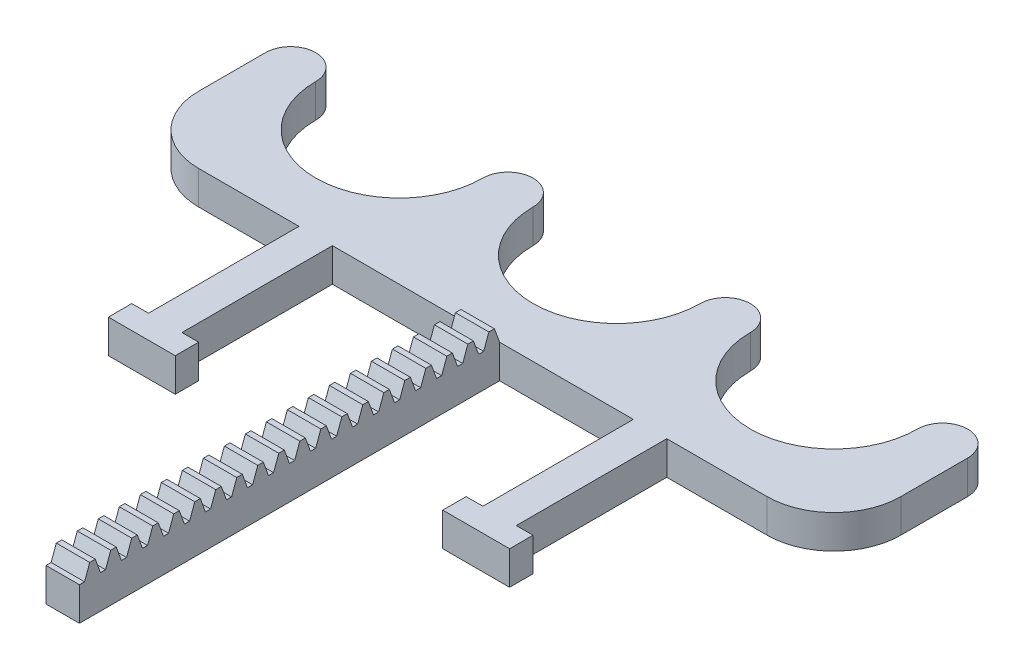
SolidWorks part; units mm, degrees
ref_plane "Plan de face" through (0, 0, 0) normal (0, 0, 1) x (1, 0, 0)
ref_plane "Plan de dessus" through (0, 0, 0) normal (0, 1, 0) x (1, 0, 0)
ref_plane "Plan de droite" through (0, 0, 0) normal (1, 0, 0) x (0, 0, -1)
sketch "Esquisse1" plane through (0, 0, 0) normal (0, 1, 0) x (1, 0, 0)
  line L0 (130, 40) -> (145, 40) construction
  line L1 (0, 0) -> (210, 0)
  line L2 (0, 0) -> (0, 40)
  line L3 (0, 40) -> (15, 40) construction
  line L4 (210, 0) -> (210, 40)
  line L5 (195, 40) -> (210, 40) construction
  line L6 (15, 40) -> (65, 40) construction
  line L7 (80, 40) -> (130, 40) construction
  line L8 (145, 40) -> (195, 40) construction
  line L9 (65, 40) -> (80, 40) construction
  arc A0 (15, 40) -> (65, 40) centre (40, 40) ccw
  arc A1 (80, 40) -> (130, 40) centre (105, 40) ccw
  arc A2 (145, 40) -> (195, 40) centre (170, 40) ccw
  arc A3 (130, 40) -> (145, 40) centre (137.5, 40) cw
  arc A4 (195, 40) -> (210, 40) centre (202.5, 40) cw
  arc A5 (65, 40) -> (80, 40) centre (72.5, 40) cw
  arc A6 (0, 40) -> (15, 40) centre (7.5, 40) cw
  point P17 (105, 40)
  point P19 (170, 40)
  dimension "D2" = 25
  dimension "D4" = 25
  dimension "D5" = 25
  dimension "D1" = 15
  dimension "D3" = 40
  dimension "D6" = 15
  dimension "D7" = 15
  dimension "D8" = 15
extrude "Boss.-Extru.1" add sketch "Esquisse1" along normal blind 10
sketch "Esquisse2" plane through (0, 10, 0) normal (0, 1, 0) x (1, 0, 0)
  line L0 (0, 0) -> (210, 0) construction
  line L1 (50, 0) -> (60, 0)
  line L2 (50, 0) -> (50, -45)
  line L3 (50, -45) -> (60, -45)
  line L4 (60, 0) -> (60, -45)
  line L5 (0, 40) -> (0, 0) construction
  line L6 (150, 0) -> (160, 0)
  line L7 (150, 0) -> (150, -45)
  line L8 (150, -45) -> (160, -45)
  line L9 (160, 0) -> (160, -45)
  line L10 (100, 0) -> (110, 0)
  line L11 (100, 0) -> (100, -45)
  line L12 (100, -45) -> (110, -45)
  line L13 (110, 0) -> (110, -45)
  line L14 (210, 0) -> (210, 40) construction
  line L16 (45, -45) -> (65, -45)
  line L17 (45, -45) -> (45, -52)
  line L18 (45, -52) -> (65, -52)
  line L19 (65, -45) -> (65, -52)
  line L24 (145, -45) -> (165, -45)
  line L25 (145, -45) -> (145, -52)
  line L26 (145, -52) -> (165, -52)
  line L27 (165, -45) -> (165, -52)
  point P18 (105, 0)
  point P19 (105, 0)
  point P24 (55, -45)
  point P25 (55, -45)
  point P36 (155, -45)
  point P37 (155, -45)
  dimension "D1" = 10
  dimension "D2" = 10
  dimension "D3" = 10
  dimension "D4" = 45
  dimension "D5" = 50
  dimension "D6" = 50
  dimension "D7" = 7
  dimension "D8" = 20
extrude "Boss.-Extru.2" add sketch "Esquisse2" against normal blind 10
fillet "Congé1" radius 20 2 edges at (210, 5, 0) (0, 5, 0)
sketch "Esquisse3" plane through (100, 0, 0) normal (-1, 0, 0) x (0, 0, 1)
  line L0 (2.378, 14.25) -> (2.378, 12.25) construction
  line L1 (-2.1293, 12.25) -> (5.817, 12.25) construction
  line L2 (2.378, 12.25) -> (5.4445, 13.3661) construction
  line L3 (3.209, 14.25) -> (4.7559, 10)
  line L4 (1.5469, 14.25) -> (0, 10)
  line L5 (1.5469, 14.25) -> (3.209, 14.25)
  line L6 (0, 10) -> (6.283, 10) construction
  line L7 (4.7559, 10) -> (6.283, 10)
  line L8 (7.8299, 14.25) -> (9.492, 14.25)
  line L9 (7.8299, 14.25) -> (6.283, 10)
  line L10 (9.492, 14.25) -> (11.0389, 10)
  line L11 (11.0389, 10) -> (12.566, 10)
  line L12 (14.1129, 14.25) -> (15.775, 14.25)
  line L13 (14.1129, 14.25) -> (12.566, 10)
  line L14 (15.775, 14.25) -> (17.3219, 10)
  line L15 (17.3219, 10) -> (18.849, 10)
  line L16 (20.3959, 14.25) -> (22.058, 14.25)
  line L17 (20.3959, 14.25) -> (18.849, 10)
  line L18 (22.058, 14.25) -> (23.6049, 10)
  line L19 (23.6049, 10) -> (25.132, 10)
  line L20 (26.6789, 14.25) -> (28.341, 14.25)
  line L21 (26.6789, 14.25) -> (25.132, 10)
  line L22 (28.341, 14.25) -> (29.8879, 10)
  line L23 (29.8879, 10) -> (31.415, 10)
  line L24 (32.9619, 14.25) -> (34.624, 14.25)
  line L25 (32.9619, 14.25) -> (31.415, 10)
  line L26 (34.624, 14.25) -> (36.1709, 10)
  line L27 (36.1709, 10) -> (37.698, 10)
  line L28 (39.2449, 14.25) -> (40.907, 14.25)
  line L29 (39.2449, 14.25) -> (37.698, 10)
  line L30 (40.907, 14.25) -> (42.4539, 10)
  line L31 (42.4539, 10) -> (43.981, 10)
  line L32 (0, 10) -> (0, 0)
  line L33 (0, 0) -> (125.66, 0)
  line L35 (45.5279, 14.25) -> (47.19, 14.25)
  line L36 (45.5279, 14.25) -> (43.981, 10)
  line L37 (47.19, 14.25) -> (48.7369, 10)
  line L38 (48.7369, 10) -> (50.264, 10)
  line L39 (51.8109, 14.25) -> (53.473, 14.25)
  line L40 (51.8109, 14.25) -> (50.264, 10)
  line L41 (53.473, 14.25) -> (55.0199, 10)
  line L42 (55.0199, 10) -> (56.547, 10)
  line L43 (58.0939, 14.25) -> (59.756, 14.25)
  line L44 (58.0939, 14.25) -> (56.547, 10)
  line L45 (59.756, 14.25) -> (61.3029, 10)
  line L46 (61.3029, 10) -> (62.83, 10)
  line L47 (64.3769, 14.25) -> (66.039, 14.25)
  line L48 (64.3769, 14.25) -> (62.83, 10)
  line L49 (66.039, 14.25) -> (67.5859, 10)
  line L50 (67.5859, 10) -> (69.113, 10)
  line L51 (70.6599, 14.25) -> (72.322, 14.25)
  line L52 (70.6599, 14.25) -> (69.113, 10)
  line L53 (72.322, 14.25) -> (73.8689, 10)
  line L54 (73.8689, 10) -> (75.396, 10)
  line L55 (76.9429, 14.25) -> (78.605, 14.25)
  line L56 (76.9429, 14.25) -> (75.396, 10)
  line L57 (78.605, 14.25) -> (80.1519, 10)
  line L58 (80.1519, 10) -> (81.679, 10)
  line L59 (83.2259, 14.25) -> (84.888, 14.25)
  line L60 (83.2259, 14.25) -> (81.679, 10)
  line L61 (84.888, 14.25) -> (86.4349, 10)
  line L62 (86.4349, 10) -> (87.962, 10)
  line L63 (89.5089, 14.25) -> (91.171, 14.25)
  line L64 (89.5089, 14.25) -> (87.962, 10)
  line L65 (91.171, 14.25) -> (92.7179, 10)
  line L66 (92.7179, 10) -> (94.245, 10)
  line L67 (95.7919, 14.25) -> (97.454, 14.25)
  line L68 (95.7919, 14.25) -> (94.245, 10)
  line L69 (97.454, 14.25) -> (99.0009, 10)
  line L70 (99.0009, 10) -> (100.528, 10)
  line L71 (102.0749, 14.25) -> (103.737, 14.25)
  line L72 (102.0749, 14.25) -> (100.528, 10)
  line L73 (103.737, 14.25) -> (105.2839, 10)
  line L74 (105.2839, 10) -> (106.811, 10)
  line L75 (108.3579, 14.25) -> (110.02, 14.25)
  line L76 (108.3579, 14.25) -> (106.811, 10)
  line L77 (110.02, 14.25) -> (111.5669, 10)
  line L78 (111.5669, 10) -> (113.094, 10)
  line L79 (114.6409, 14.25) -> (116.303, 14.25)
  line L80 (114.6409, 14.25) -> (113.094, 10)
  line L81 (116.303, 14.25) -> (117.8499, 10)
  line L82 (117.8499, 10) -> (119.377, 10)
  line L83 (120.9239, 14.25) -> (122.586, 14.25)
  line L84 (120.9239, 14.25) -> (119.377, 10)
  line L85 (122.586, 14.25) -> (124.1329, 10)
  line L86 (124.1329, 10) -> (125.66, 10)
  line L87 (125.66, 0) -> (125.66, 10)
  circle A0 centre (2.378, 12.25) radius 1.615 construction
  circle A1 centre (2.378, 12.25) radius 1.465 construction
  dimension "D2" = 3.23
  dimension "D1" = 1.6622
  dimension "D3" = 20
  dimension "D4" = 2
  dimension "D5" = 2.25
  dimension "D6" = 6.283
  dimension "D7" = 20
  dimension "D8" = 10
extrude "Boss.-Extru.3" add sketch "Esquisse3" against normal blind 10
